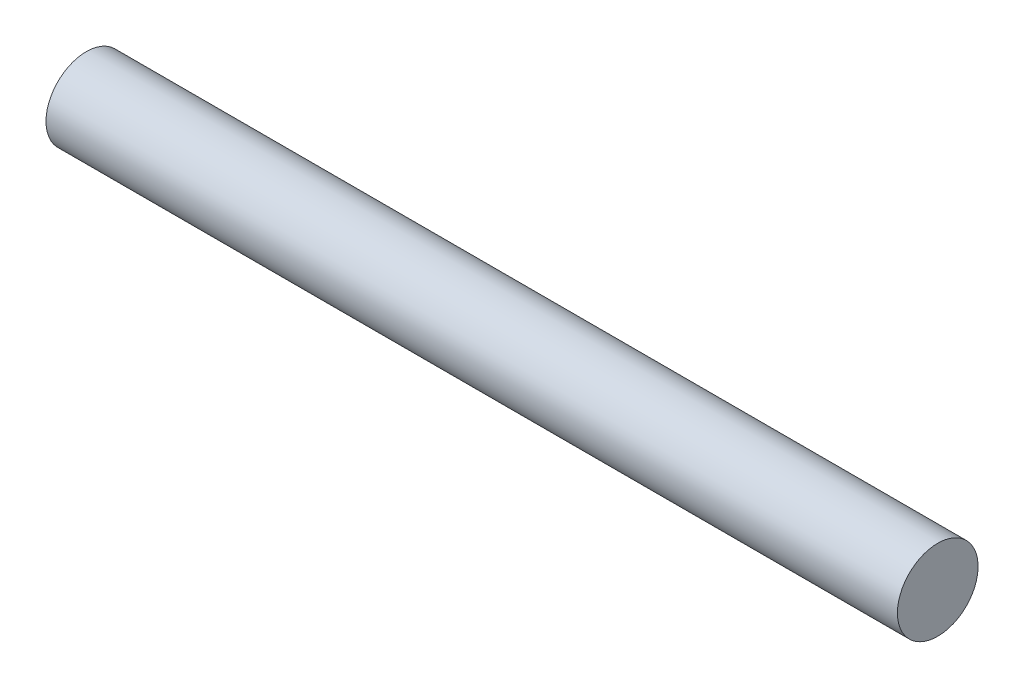
SolidWorks part; units mm, degrees
ref_plane "Ön Düzlem" through (0, 0, 0) normal (0, 0, 1) x (1, 0, 0)
ref_plane "Üst Düzlem" through (0, 0, 0) normal (0, 1, 0) x (1, 0, 0)
ref_plane "Sağ Düzlem" through (0, 0, 0) normal (1, 0, 0) x (0, 0, -1)
sketch "Çizim1" plane through (0, 0, 0) normal (0, 0, 1) x (1, 0, 0)
  line L0 (-169.6363, 451.9998) -> (20.4124, 451.9998)
  line L5 (-169.6363, 451.9998) -> (20.4124, 451.9998)
  line L6 (-169.6363, 451.9998) -> (-169.6363, 460.9998)
  line L7 (-169.6363, 460.9998) -> (20.4124, 460.9998)
  line L8 (20.4124, 451.9998) -> (20.4124, 460.9998)
  dimension "D2" = 9
revolve "Döndür1" add sketch "Çizim1" angle 360 about L0
